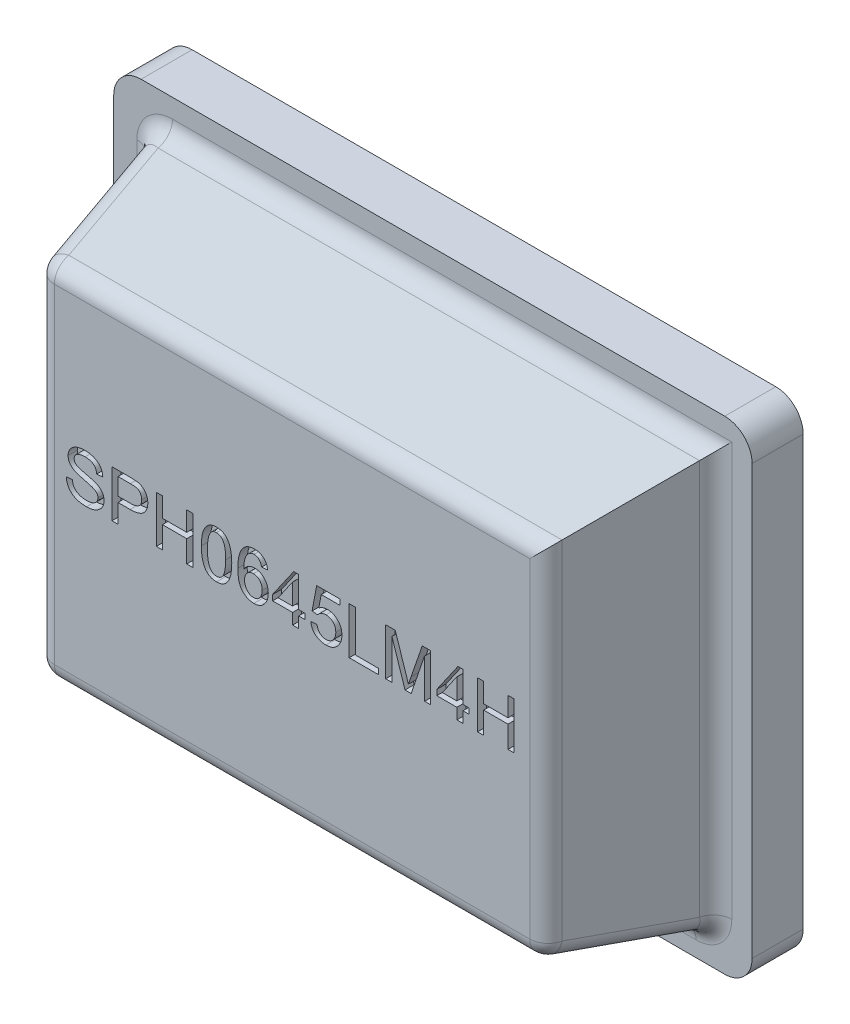
SolidWorks part; units mm, degrees
ref_plane "Plan de face" through (0, 0, 0) normal (0, 0, 1) x (1, 0, 0)
ref_plane "Plan de dessus" through (0, 0, 0) normal (0, 1, 0) x (1, 0, 0)
ref_plane "Plan de droite" through (0, 0, 0) normal (1, 0, 0) x (0, 0, -1)
sketch "Esquisse1" plane through (0, 0, 0) normal (0, 0, 1) x (1, 0, 0)
  line L1 (0.15, 0) -> (3.35, 0)
  line L2 (0, 0.15) -> (0, 2.5)
  line L3 (0.15, 2.65) -> (3.35, 2.65)
  line L4 (3.5, 0.15) -> (3.5, 2.5)
  arc A0 (0, 2.5) -> (0.15, 2.65) centre (0.15, 2.5) cw
  arc A1 (0.15, 0) -> (0, 0.15) centre (0.15, 0.15) cw
  arc A2 (3.35, 0) -> (3.5, 0.15) centre (3.35, 0.15) ccw
  arc A3 (3.35, 2.65) -> (3.5, 2.5) centre (3.35, 2.5) cw
  point P7 (0, 2.65)
  point P10 (0, 0)
  point P13 (3.5, 0)
  point P16 (3.5, 2.65)
  dimension "D3" = 0.15
  dimension "D1" = 3.5
  dimension "D2" = 2.65
extrude "Boss.-Extru.1" add sketch "Esquisse1" along normal blind 0.28
sketch "Esquisse2" plane through (0, 0, 0.28) normal (0, 0, 1) x (1, 0, 0)
  line L0 (0.0439, 2.6061) -> (3.4561, 0.0439) construction
  line L1 (3.4561, 0.0439) -> (3.4717, 2.5877) construction
  line L2 (3.4717, 2.5877) -> (0.0439, 0.0439) construction
  line L4 (0.2078, 0.1658) -> (3.3078, 0.1658)
  line L5 (0.2078, 0.1658) -> (0.2078, 2.4658)
  line L6 (0.2078, 2.4658) -> (3.3078, 2.4658)
  line L7 (3.3078, 0.1658) -> (3.3078, 2.4658)
  line L8 (0.2078, 0.1658) -> (3.3078, 2.4658) construction
  line L9 (0.2078, 2.4658) -> (3.3078, 0.1658) construction
  arc A0 (0.15, 2.65) -> (0, 2.5) centre (0.15, 2.5) ccw construction
  arc A1 (3.35, 0) -> (3.5, 0.15) centre (3.35, 0.15) ccw construction
  arc A2 (3.5, 2.5) -> (3.35, 2.65) centre (3.35, 2.5) ccw construction
  arc A3 (0, 0.15) -> (0.15, 0) centre (0.15, 0.15) ccw construction
  point P16 (1.7578, 1.3158)
  dimension "D1" = 3.1
  dimension "D2" = 2.3
extrude "Boss.-Extru.2" add sketch "Esquisse2" along normal blind 0.78 draft 12
fillet "Congé1" radius 0.1 11 edges at (1.7578, 2.4658, 0.28) (0.2078, 1.3158, 0.28) (3.3078, 1.3158, 0.28) (0.2907, 0.2487, 0.67) (1.7578, 0.3316, 1.06) (3.2249, 0.2487, 0.67) (1.7578, 0.1658, 0.28) (0.2907, 2.3829, 0.67) (1.7578, 2.3, 1.06) (3.142, 1.3158, 1.06) (0.3736, 1.3158, 1.06)
sketch "Esquisse3" plane through (0, 0, 1.06) normal (0, 0, 1) x (1, 0, 0)
  text T0 "SPH0645LM4H" font "@Arial Unicode MS" height in points 1
extrude "Enlèv. mat.-Extru.1" cut sketch "Esquisse3" against normal blind 0.05
